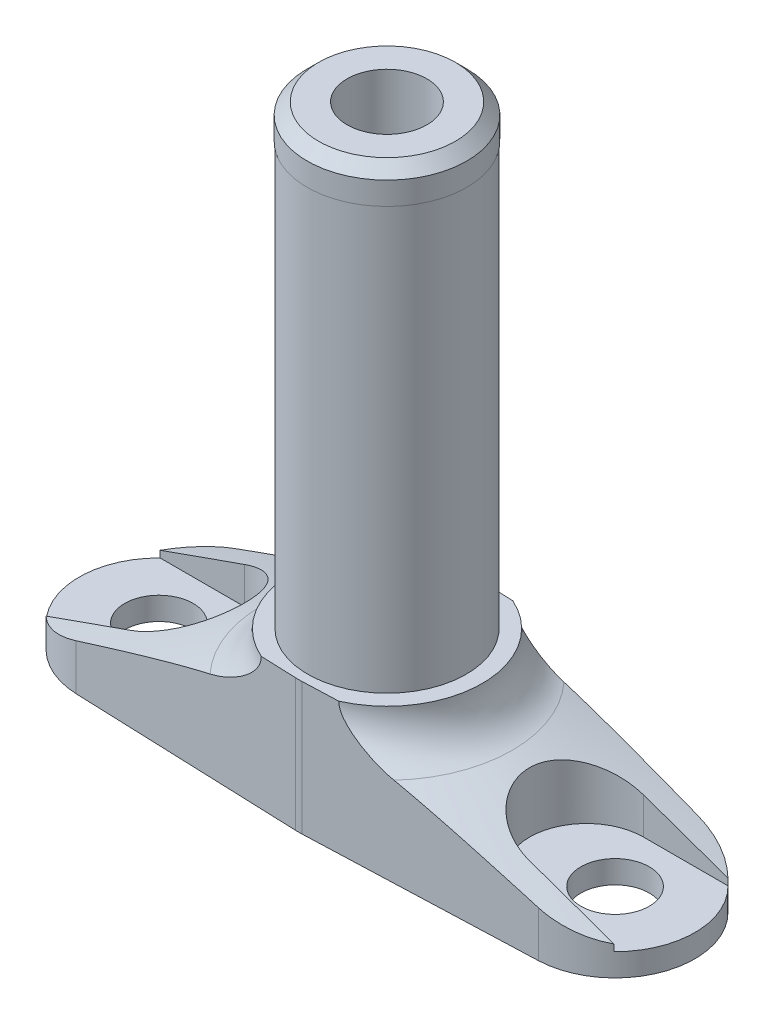
SolidWorks part; units mm, degrees
material "7075-T6 (SN)"
ref_plane "Płaszczyzna XY" through (0, 0, 0) normal (0, 0, 1) x (1, 0, 0)
ref_plane "Płaszczyzna XZ" through (0, 0, 0) normal (0, 1, 0) x (1, 0, 0)
ref_plane "Płaszczyzna YZ" through (0, 0, 0) normal (1, 0, 0) x (0, 0, -1)
sketch "Szkic1" plane through (0, 0, 0) normal (0, 0, 1) x (1, 0, 0)
  line L0 (0, 0) -> (0, 25) construction
  line L1 (0, 0) -> (0, 25)
  line L2 (0, 0) -> (27, 0)
  line L4 (0, 25) -> (27, 25)
  line L5 (27, 0) -> (27, 25)
  dimension "D1" = 54
  dimension "D2" = 25
revolve "Obrót1" add sketch "Szkic1" angle 360 about L0
sketch "Szkic2" plane through (0, 0, 0) normal (0, 0, 1) x (1, 0, 0)
  line L0 (0, 0) -> (0, 25) construction
  line L1 (27, 25) -> (-27, 25) construction
  line L2 (0, 25) -> (8.35, 25) construction
  line L3 (8.35, 25) -> (8.35, 8.788)
  line L4 (8.35, 8.788) -> (27, 2)
  line L5 (27, 0) -> (27, 25) construction
  line L6 (-27, 0) -> (27, 0) construction
  line L7 (8.35, 25) -> (27, 25)
  line L8 (27, 25) -> (27, 2)
  dimension "D1" = 2
  dimension "D2" = 20
  dimension "D3" = 16.7
revolve "Wycięcie-obrót1" cut sketch "Szkic2" angle 360 about L0
fillet "Zaokrąglenie1" radius 4 1 edges at (0, 8.788, -8.35)
ref_plane "Płaszczyzna1" through (0, 2, 0) normal (0, 1, 0) x (1, 0, 0)
sketch "Szkic4" plane through (0, 2, 0) normal (0, 1, 0) x (1, 0, 0)
  line L0 (0, 8.8242) -> (0, -11.1289) construction
  circle A0 centre (-20, 0) radius 3
  circle A1 centre (20, 0) radius 3
  dimension "D1" = 6
  dimension "D2" = 6
  dimension "D3" = 40
extrude "Wytnij-wyciągnięcie3" cut sketch "Szkic4" against normal through all and the other way through all
sketch "Szkic3" plane through (0, 2, 0) normal (0, 1, 0) x (1, 0, 0)
  line L0 (-17.5, 5) -> (-26.533, 5)
  line L13 (-17.5, -5) -> (-26.533, -5)
  line L14 (17.5, 5) -> (26.533, 5)
  line L15 (17.5, -5) -> (26.533, -5)
  line L16 (0, 21.1527) -> (0, -20.0817) construction
  arc A1 (-17.5, -5) -> (-17.5, 5) centre (-17.5, 0) ccw
  arc A2 (17.5, 5) -> (17.5, -5) centre (17.5, 0) ccw
  circle A3 centre (0, 0) radius 27 construction
  arc A4 (-26.533, 5) -> (-26.533, -5) centre (0, 0) ccw
  arc A5 (26.533, -5) -> (26.533, 5) centre (0, 0) ccw
  dimension "D1" = 10
  dimension "D2" = 10
  dimension "D3" = 35
extrude "Wytnij-wyciągnięcie2" cut sketch "Szkic3" along normal through all
sketch "Szkic5" plane through (0, 0, 0) normal (0, -1, 0) x (1, 0, 0)
  line L0 (-20.2625, 6.9951) -> (-0.2906, 7.7445)
  line L1 (-20.2625, -6.9951) -> (-0.2906, -7.7445)
  line L2 (0.2906, 7.7445) -> (20.2625, 6.9951)
  line L3 (20.2625, -6.9951) -> (0.2906, -7.7445)
  arc A0 (-0.2906, -7.7445) -> (0.2906, -7.7445) centre (0, 0) ccw
  arc A1 (-20.2625, 6.9951) -> (-20.2625, -6.9951) centre (-20, 0) ccw
  arc A2 (20.2625, -6.9951) -> (20.2625, 6.9951) centre (20, 0) ccw
  circle A3 centre (0, 0) radius 27 construction
  arc A4 (0.2906, 7.7445) -> (-0.2906, 7.7445) centre (0, 0) ccw
  dimension "D1" = 15.5
extrude "Wytnij-wyciągnięcie4" cut sketch "Szkic5" against normal through all flip side to cut
sketch "Szkic8" plane through (0, 0, 0) normal (0, 0, 1) x (1, 0, 0)
  line L2 (0, 25) -> (0, 11.5889)
  line L5 (0, 11.5889) -> (8.35, 11.5889)
  line L6 (8.35, 11.5889) -> (8.35, 25) construction
  line L7 (8.35, 11.5889) -> (8.35, 25)
  line L8 (8.35, 25) -> (0, 25)
  line L9 (8.35, 11.5889) -> (3.3965, 11.5889) construction
  dimension "D1" = 0
revolve "Wycięcie-obrót2" cut sketch "Szkic8" angle 360 about L2
sketch "Szkic9" plane through (0, 0, 0) normal (0, 0, 1) x (1, 0, 0)
  line L2 (0, 11.5889) -> (0, 51.5889) construction
  line L3 (0, 51.5889) -> (6, 51.5889)
  line L5 (6, 51.5889) -> (7, 50.5889)
  line L6 (0, 51.5889) -> (7, 51.5889)
  line L7 (0, 51.5889) -> (0, 52.4234) construction
  line L8 (6.95, 48.5889) -> (7, 48.5889)
  line L9 (7, 50.5889) -> (7, 48.5889)
  line L10 (0, 11.5889) -> (0, 51.5889)
  line L11 (0.2906, 11.5889) -> (-0.2906, 11.5889) construction
  line L12 (6.95, 48.5889) -> (6.95, 11.5889)
  line L13 (6.95, 11.5889) -> (0, 11.5889)
  dimension "D1" = 0
  dimension "D2" = 40
  dimension "D3" = 14
  dimension "D4" = 3
revolve "Obrót2" add sketch "Szkic9" angle 360 about L2
sketch "Szkic10" plane through (0, 51.5889, 0) normal (0, 1, 0) x (1, 0, 0)
  circle A0 centre (0, 0) radius 3.5
  dimension "D1" = 7
extrude "Wytnij-wyciągnięcie5" cut sketch "Szkic10" against normal through all
equation "\"D3@Szkic3\"=40-2*1/2*5"
